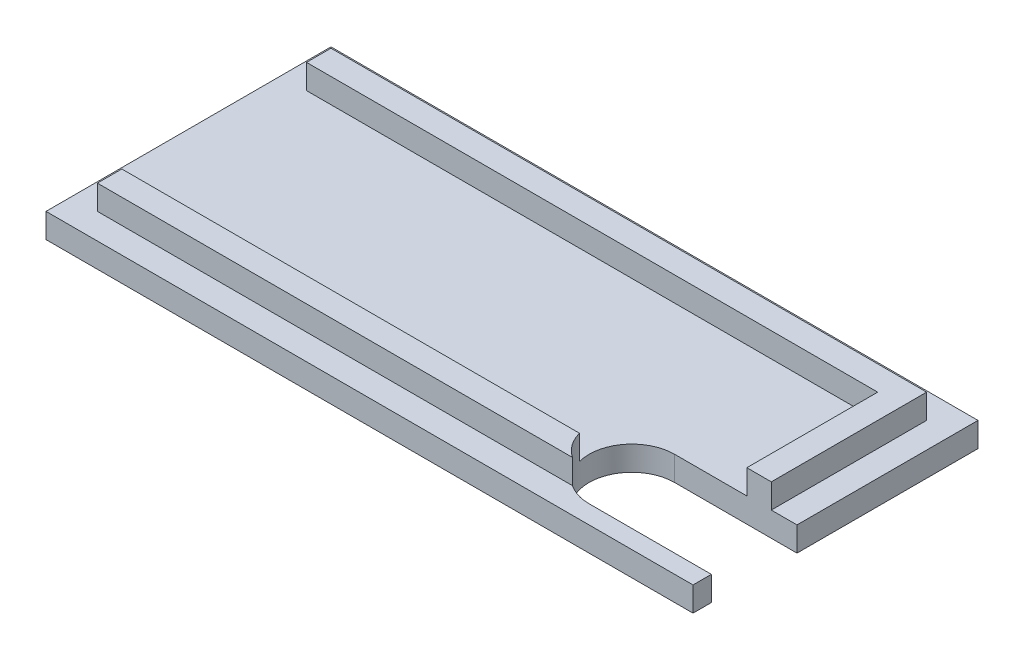
SolidWorks part; units mm, degrees
ref_plane "Front Plane" through (0, 0, 0) normal (0, 0, 1) x (1, 0, 0)
ref_plane "Top Plane" through (0, 0, 0) normal (0, 1, 0) x (1, 0, 0)
ref_plane "Right Plane" through (0, 0, 0) normal (1, 0, 0) x (0, 0, -1)
sketch "Sketch1" plane through (0, 0, 0) normal (0, 1, 0) x (1, 0, 0)
  line L1 (0, 0) -> (52.9, 0)
  line L2 (0, 0) -> (0, 23.3)
  line L3 (0, 23.3) -> (52.9, 23.3)
  line L4 (52.9, 0) -> (52.9, 23.3)
  line L5 (0, 0) -> (52.9, 23.3) construction
  line L6 (0, 23.3) -> (52.9, 0) construction
  point P4 (26.45, 11.65)
  dimension "D1" = 23.3
  dimension "D2" = 52.9
extrude "Boss-Extrude1" add sketch "Sketch1" along normal blind 2
sketch "Sketch2" plane through (0, 2, 0) normal (0, 1, 0) x (1, 0, 0)
  line L0 (0, 23.3) -> (0, 0) construction
  line L1 (2.1, 21.2) -> (50.8, 21.2)
  line L2 (2.1, 21.2) -> (2.1, 19.2)
  line L3 (2.1, 2.1) -> (50.8, 2.1)
  line L4 (50.8, 21.2) -> (50.8, 2.1)
  line L5 (2.1, 21.2) -> (50.8, 2.1) construction
  line L6 (2.1, 2.1) -> (50.8, 21.2) construction
  line L7 (4.1, 19.2) -> (48.8, 19.2)
  line L8 (4.1, 19.2) -> (4.1, 4.1) construction
  line L9 (4.1, 4.1) -> (48.8, 4.1)
  line L10 (48.8, 19.2) -> (48.8, 4.1)
  line L11 (4.1, 19.2) -> (48.8, 4.1) construction
  line L12 (4.1, 4.1) -> (48.8, 19.2) construction
  line L13 (52.9, 0) -> (52.9, 23.3) construction
  line L14 (52.9, 23.3) -> (0, 23.3) construction
  line L15 (0, 0) -> (52.9, 0) construction
  line L16 (4.1, 19.2) -> (2.1, 19.2)
  line L17 (4.1, 4.1) -> (2.1, 4.1)
  line L18 (2.1, 19.2) -> (2.1, 4.1) construction
  line L19 (2.1, 4.1) -> (2.1, 2.1)
  point P4 (26.45, 11.65)
  point P9 (26.45, 11.65)
  dimension "D1" = 2
  dimension "D2" = 2
  dimension "D3" = 2.1
  dimension "D4" = 2.1
  dimension "D5" = 2.1
  dimension "D6" = 2.1
extrude "Boss-Extrude2" add sketch "Sketch2" along normal blind 2
sketch "Sketch3" plane through (0, 0, 0) normal (0, -1, 0) x (1, 0, 0)
  line L0 (52.9, -5) -> (42.9, -5) construction
  line L1 (52.9, 0) -> (52.9, -23.3) construction
  line L2 (42.9, -5) -> (53.2352, -5) construction
  line L3 (42.9, -1.5) -> (53.2352, -1.5)
  line L4 (42.9, -8.5) -> (53.2352, -8.5)
  line L5 (0, 0) -> (52.9, 0) construction
  arc A0 (42.9, -1.5) -> (42.9, -8.5) centre (42.9, -5) ccw
  arc A1 (53.2352, -8.5) -> (53.2352, -1.5) centre (53.2352, -5) ccw
  point P4 (48.0676, -5)
  dimension "D1" = 7
  dimension "D2" = 5
  dimension "D3" = 10
extrude "Cut-Extrude1" cut sketch "Sketch3" against normal through all
